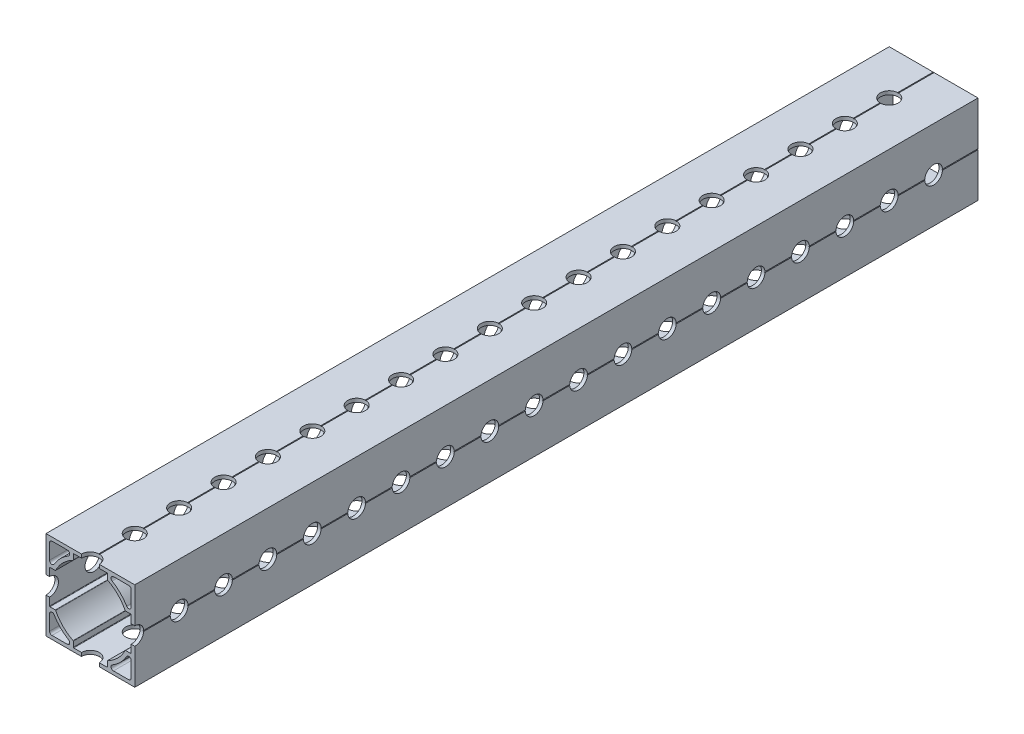
SolidWorks part; units mm, degrees
material "6061 Alloy"
ref_plane "Front Plane" through (0, 0, 0) normal (0, 0, 1) x (1, 0, 0)
ref_plane "Top Plane" through (0, 0, 0) normal (0, 1, 0) x (1, 0, 0)
ref_plane "Right Plane" through (0, 0, 0) normal (1, 0, 0) x (0, 0, -1)
other "Configuration Table"
sketch "Sketch1" plane through (0, 0, 0) normal (0, 0, 1) x (1, 0, 0)
  line L6 (1.7076, 1.016) -> (6.1029, 1.016)
  line L7 (1.016, 6.1029) -> (1.016, 1.7076)
  line L10 (25.4, 12.827) -> (25.4, 25.4)
  line L11 (25.4, 25.4) -> (12.827, 25.4)
  line L14 (12.573, 25.4) -> (0, 25.4)
  line L15 (0, 25.4) -> (0, 12.827)
  line L16 (0, 12.827) -> (0.127, 12.7)
  line L17 (0.127, 12.7) -> (0, 12.573)
  line L18 (0, 12.573) -> (0, 0)
  line L22 (12.827, 0) -> (25.4, 0)
  line L23 (25.4, 0) -> (25.4, 12.573)
  line L24 (1.143, 7.8105) -> (2.6421, 7.8105)
  line L25 (1.016, 17.4625) -> (1.016, 7.9375)
  line L26 (2.6421, 17.5895) -> (1.143, 17.5895)
  line L27 (1.016, 23.6924) -> (1.016, 19.2971)
  line L28 (6.1029, 24.384) -> (1.7076, 24.384)
  line L29 (17.5895, 22.7579) -> (17.5895, 24.257)
  line L30 (17.4625, 24.384) -> (7.9375, 24.384)
  line L31 (7.8105, 24.257) -> (7.8105, 22.7579)
  line L32 (23.6924, 24.384) -> (19.2971, 24.384)
  line L33 (24.384, 19.2971) -> (24.384, 23.6924)
  line L34 (22.7579, 7.8105) -> (24.257, 7.8105)
  line L35 (24.384, 7.9375) -> (24.384, 17.4625)
  line L36 (24.257, 17.5895) -> (22.7579, 17.5895)
  line L37 (24.384, 1.7076) -> (24.384, 6.1029)
  line L38 (19.2971, 1.016) -> (23.6924, 1.016)
  line L39 (7.8105, 2.6421) -> (7.8105, 1.143)
  line L40 (7.9375, 1.016) -> (17.4625, 1.016)
  line L41 (17.5895, 1.143) -> (17.5895, 2.6421)
  line L44 (12.827, 25.4) -> (12.7, 25.273)
  line L45 (12.7, 25.273) -> (12.573, 25.4)
  line L46 (25.4, 12.573) -> (25.273, 12.7)
  line L47 (25.273, 12.7) -> (25.4, 12.827)
  line L48 (12.573, 0) -> (12.7, 0.127)
  line L49 (12.7, 0.127) -> (12.827, 0)
  line L50 (12.573, 0) -> (0, 0)
  arc A14 (1.016, 1.7076) -> (1.7076, 1.016) centre (1.7076, 1.7076) ccw
  arc A15 (2.3006, 6.4588) -> (1.016, 6.1029) centre (1.7076, 6.1029) ccw
  arc A16 (2.3006, 6.4588) -> (6.4588, 2.3006) centre (12.7, 12.7) ccw
  arc A17 (6.1029, 1.016) -> (6.4588, 2.3006) centre (6.1029, 1.7076) ccw
  arc A18 (2.7558, 7.7402) -> (7.7402, 2.7558) centre (12.7, 12.7) ccw
  arc A19 (2.7558, 7.7402) -> (2.6421, 7.8105) centre (2.6421, 7.6835) ccw
  arc A20 (1.016, 7.9375) -> (1.143, 7.8105) centre (1.143, 7.9375) ccw
  arc A21 (1.143, 17.5895) -> (1.016, 17.4625) centre (1.143, 17.4625) ccw
  arc A22 (2.6421, 17.5895) -> (2.7558, 17.6598) centre (2.6421, 17.7165) ccw
  arc A23 (1.016, 19.2971) -> (2.3006, 18.9412) centre (1.7076, 19.2971) ccw
  arc A24 (6.4588, 23.0994) -> (2.3006, 18.9412) centre (12.7, 12.7) ccw
  arc A25 (6.4588, 23.0994) -> (6.1029, 24.384) centre (6.1029, 23.6924) ccw
  arc A26 (1.7076, 24.384) -> (1.016, 23.6924) centre (1.7076, 23.6924) ccw
  arc A27 (17.5895, 24.257) -> (17.4625, 24.384) centre (17.4625, 24.257) ccw
  arc A28 (17.5895, 22.7579) -> (17.6598, 22.6442) centre (17.7165, 22.7579) ccw
  arc A29 (7.9375, 24.384) -> (7.8105, 24.257) centre (7.9375, 24.257) ccw
  arc A30 (7.7402, 22.6442) -> (7.8105, 22.7579) centre (7.6835, 22.7579) ccw
  arc A31 (7.7402, 22.6442) -> (2.7558, 17.6598) centre (12.7, 12.7) ccw
  arc A32 (19.2971, 24.384) -> (18.9412, 23.0994) centre (19.2971, 23.6924) ccw
  arc A33 (23.0994, 18.9412) -> (18.9412, 23.0994) centre (12.7, 12.7) ccw
  arc A34 (23.0994, 18.9412) -> (24.384, 19.2971) centre (23.6924, 19.2971) ccw
  arc A35 (24.384, 23.6924) -> (23.6924, 24.384) centre (23.6924, 23.6924) ccw
  arc A36 (24.257, 7.8105) -> (24.384, 7.9375) centre (24.257, 7.9375) ccw
  arc A37 (22.7579, 7.8105) -> (22.6442, 7.7402) centre (22.7579, 7.6835) ccw
  arc A38 (24.384, 17.4625) -> (24.257, 17.5895) centre (24.257, 17.4625) ccw
  arc A39 (22.6442, 17.6598) -> (22.7579, 17.5895) centre (22.7579, 17.7165) ccw
  arc A40 (22.6442, 17.6598) -> (17.6598, 22.6442) centre (12.7, 12.7) ccw
  arc A41 (24.384, 6.1029) -> (23.0994, 6.4588) centre (23.6924, 6.1029) ccw
  arc A42 (18.9412, 2.3006) -> (23.0994, 6.4588) centre (12.7, 12.7) ccw
  arc A43 (18.9412, 2.3006) -> (19.2971, 1.016) centre (19.2971, 1.7076) ccw
  arc A44 (23.6924, 1.016) -> (24.384, 1.7076) centre (23.6924, 1.7076) ccw
  arc A45 (7.8105, 1.143) -> (7.9375, 1.016) centre (7.9375, 1.143) ccw
  arc A46 (7.8105, 2.6421) -> (7.7402, 2.7558) centre (7.6835, 2.6421) ccw
  arc A47 (17.4625, 1.016) -> (17.5895, 1.143) centre (17.4625, 1.143) ccw
  arc A48 (17.6598, 2.7558) -> (17.5895, 2.6421) centre (17.7165, 2.6421) ccw
  arc A49 (17.6598, 2.7558) -> (22.6442, 7.7402) centre (12.7, 12.7) ccw
  point P41 (12.7, 24.384)
  point P109 (12.7, 12.7)
  point P116 (12.7, 12.7)
  dimension "D1" = 25.4
  dimension "D2" = 1.016
  dimension "D3" = 4
  dimension "D4" = 1.016
  dimension "D7" = 0.127
  dimension "D12" = 11.1125
  dimension "D5" = 0.127
  dimension "D13" = 12.1285
  dimension "D6" = 9.525
  dimension "D8" = 135
  dimension "D9" = 5.7785
  dimension "D10" = 0.127
  dimension "D11" = 4
extrude "Boss-Extrude1" add sketch "Sketch1" along normal blind 241.3
sketch "Sketch2" plane through (0, 0, 0) normal (-1, 0, 0) x (0, 0, 1)
  line L0 (241.3, 12.7) -> (0, 12.7) construction
  line L1 (0, 12.573) -> (0, 0) construction
  circle A0 centre (12.7, 12.7) radius 2.54
  dimension "D1" = 5.08
  dimension "D2" = 12.7
extrude "Cut-Extrude1" cut sketch "Sketch2" against normal through all
pattern_circular "CirPattern1" count 4 over 360 about axis through (12.7, 12.7, 241.3) along (0, 0, -1) of "Cut-Extrude1"
pattern_linear "LPattern1" count 95 spacing 12.7 along (0, 0, 1) of "CirPattern1", "Cut-Extrude1"
equation "\"Length\"= 9.5"
equation "\"D1@Boss-Extrude1\"=\"Length\""
